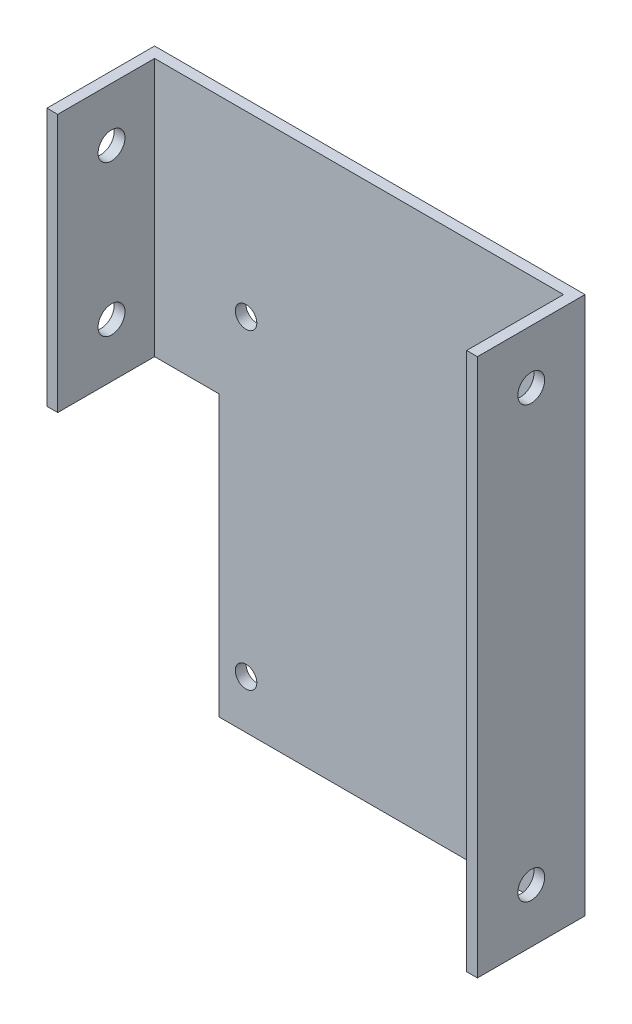
SolidWorks part; units mm, degrees
ref_plane "Alzado" through (0, 0, 0) normal (0, 0, 1) x (1, 0, 0)
ref_plane "Planta" through (0, 0, 0) normal (0, 1, 0) x (1, 0, 0)
ref_plane "Vista lateral" through (0, 0, 0) normal (1, 0, 0) x (0, 0, -1)
sketch "Sketch1" plane through (0, 0, 0) normal (0, 0, 1) x (1, 0, 0)
  line L1 (-15.7576, 19.8268) -> (24.2424, 19.8268)
  line L2 (-15.7576, 19.8268) -> (-15.7576, -30.1732)
  line L3 (-15.7576, -30.1732) -> (24.2424, -30.1732)
  line L4 (24.2424, 19.8268) -> (24.2424, -30.1732)
  dimension "D1" = 40
  dimension "D2" = 50
extrude "Boss-Extrude1" add sketch "Sketch1" along normal blind 1
sketch "Sketch2" plane through (0, 0, 1) normal (0, 0, 1) x (1, 0, 0)
  line L1 (-15.7576, -30.1732) -> (-10.7576, -30.1732)
  line L2 (-15.7576, -30.1732) -> (-15.7576, -5.1732)
  line L3 (-15.7576, -5.1732) -> (-10.7576, -5.1732)
  line L4 (-10.7576, -30.1732) -> (-10.7576, -5.1732)
  dimension "D1" = 5
  dimension "D2" = 25
extrude "Cut-Extrude1" cut sketch "Sketch2" against normal blind 1
sketch "Sketch3" plane through (0, 0, 0) normal (0, 0, -1) x (-1, 0, 0)
  line L0 (10.7576, -5.1732) -> (15.7576, -5.1732) construction
  line L1 (15.7576, 19.8268) -> (14.7576, 19.8268)
  line L2 (15.7576, 19.8268) -> (15.7576, -5.1732)
  line L3 (15.7576, -5.1732) -> (14.7576, -5.1732)
  line L4 (14.7576, 19.8268) -> (14.7576, -5.1732)
  line L6 (-24.2424, 19.8268) -> (-23.2424, 19.8268)
  line L7 (-24.2424, 19.8268) -> (-24.2424, -5.1732)
  line L8 (-24.2424, -5.1732) -> (-23.2424, -5.1732)
  line L9 (-23.2424, 19.8268) -> (-23.2424, -5.1732)
  dimension "D1" = 1
  dimension "D2" = 1
extrude "Boss-Extrude2" add sketch "Sketch3" against normal blind 10
sketch "Sketch4" plane through (24.2424, 0, 0) normal (1, 0, 0) x (0, 0, -1)
  line L0 (-10, 19.8268) -> (-10, -5.1732) construction
  line L1 (-10, -5.1732) -> (-1, -5.1732) construction
  line L2 (-10, 19.8268) -> (0, 19.8268) construction
  circle A0 centre (-5, -0.1732) radius 1.25
  circle A1 centre (-5, 14.8268) radius 1.25
  dimension "D1" = 2.5
  dimension "D4" = 2.5
  dimension "D2" = 5
  dimension "D3" = 5
  dimension "5" = 5
extrude "Cut-Extrude3" cut sketch "Sketch4" against normal blind 63
sketch "Sketch5" plane through (24.2424, 0, 0) normal (1, 0, 0) x (0, 0, -1)
  circle A0 centre (-5, -0.1732) radius 1.25
extrude "Boss-Extrude3" add sketch "Sketch5" against normal blind 1
sketch "Sketch6" plane through (0, 0, 10) normal (0, 0, 1) x (1, 0, 0)
  line L0 (-15.7576, -5.1732) -> (-15.7576, 19.8268) construction
  line L1 (24.2424, -5.1732) -> (-15.7576, -5.1732)
  line L2 (24.2424, -5.1732) -> (24.2424, 4.8268)
  line L3 (24.2424, 4.8268) -> (-15.7576, 4.8268)
  line L4 (-15.7576, -5.1732) -> (-15.7576, 4.8268)
  dimension "D1" = 10
extrude "Cut-Extrude4" cut sketch "Sketch6" against normal blind 9
sketch "Sketch7" plane through (-15.7576, 0, 0) normal (-1, 0, 0) x (0, 0, 1)
  line L0 (1, 4.8268) -> (10, 4.8268) construction
  circle A0 centre (5, 9.8268) radius 1.25
  dimension "D1" = 2.5
  dimension "D2" = 5
extrude "Cut-Extrude5" cut sketch "Sketch7" against normal blind 53
sketch "Sketch8" plane through (0, 0, 1) normal (0, 0, 1) x (1, 0, 0)
  line L0 (-10.7576, -30.1732) -> (24.2424, -30.1732) construction
  line L1 (-10.7576, -5.1732) -> (-8.7576, -5.1732)
  line L2 (-10.7576, -5.1732) -> (-10.7576, -30.1732)
  line L3 (-10.7576, -30.1732) -> (-8.7576, -30.1732)
  line L4 (-8.7576, -5.1732) -> (-8.7576, -30.1732)
  dimension "D1" = 2
extrude "Cut-Extrude6" cut sketch "Sketch8" against normal blind 53
sketch "Sketch9" plane through (0, 0, 1) normal (0, 0, 1) x (1, 0, 0)
  line L0 (-8.7576, -30.1732) -> (-8.7576, -5.1732) construction
  line L1 (-15.7576, -5.1732) -> (-8.7576, -5.1732)
  line L2 (-15.7576, -5.1732) -> (-15.7576, -3.1732)
  line L3 (-15.7576, -3.1732) -> (-8.7576, -3.1732)
  line L4 (-8.7576, -5.1732) -> (-8.7576, -3.1732)
  dimension "D1" = 2
extrude "Cut-Extrude8" cut sketch "Sketch9" against normal blind 53
sketch "Sketch10" plane through (24.2424, 0, 0) normal (1, 0, 0) x (0, 0, -1)
  line L0 (-1, -30.1732) -> (-1, 4.8268) construction
  line L1 (-10, 4.8268) -> (-1, 4.8268)
  line L2 (-10, 4.8268) -> (-10, -15.8236)
  line L3 (-10, -15.8236) -> (-1, -15.8236)
  line L4 (-1, 4.8268) -> (-1, -15.8236)
extrude "Boss-Extrude4" add sketch "Sketch10" against normal blind 1
sketch "Sketch11" plane through (24.2424, 0, 0) normal (1, 0, 0) x (0, 0, -1)
  line L0 (-10, -15.8236) -> (-1, -15.8236) construction
  line L1 (0, -30.1732) -> (0, 19.8268) construction
  circle A0 centre (-5, -10.8236) radius 1.25
  dimension "D1" = 5
  dimension "D2" = 5
extrude "Cut-Extrude9" cut sketch "Sketch11" against normal blind 1
sketch "Sketch12" plane through (24.2424, 0, 0) normal (1, 0, 0) x (0, 0, -1)
  circle A0 centre (-5, 9.8268) radius 1.25
extrude "Boss-Extrude5" add sketch "Sketch12" against normal blind 1
sketch "Sketch13" plane through (-15.7576, 0, 0) normal (-1, 0, 0) x (0, 0, 1)
  circle A0 centre (5, 9.8268) radius 1.25
extrude "Boss-Extrude6" add sketch "Sketch13" against normal blind 1
sketch "Sketch14" plane through (0, 0, 1) normal (0, 0, 1) x (1, 0, 0)
  line L0 (-8.7576, -30.1732) -> (-8.7576, -3.1732) construction
  line L1 (-15.7576, -3.1732) -> (-8.7576, -3.1732)
  line L2 (-15.7576, -3.1732) -> (-15.7576, -4.1732)
  line L3 (-15.7576, -4.1732) -> (-8.7576, -4.1732)
  line L4 (-8.7576, -3.1732) -> (-8.7576, -4.1732)
  dimension "D1" = 1
extrude "Boss-Extrude7" add sketch "Sketch14" against normal blind 1
sketch "Sketch15" plane through (0, 0, 1) normal (0, 0, 1) x (1, 0, 0)
  line L1 (-15.7576, -4.1732) -> (-14.7576, -4.1732)
  line L2 (-15.7576, -4.1732) -> (-15.7576, 4.8268)
  line L3 (-15.7576, 4.8268) -> (-14.7576, 4.8268)
  line L4 (-14.7576, -4.1732) -> (-14.7576, 4.8268)
extrude "Boss-Extrude8" add sketch "Sketch15" along normal blind 9
sketch "Sketch16" plane through (-15.7576, 0, 0) normal (-1, 0, 0) x (0, 0, 1)
  line L0 (0, -4.1732) -> (10, -4.1732) construction
  circle A0 centre (5, 14.8268) radius 1.25
  circle A1 centre (5, 0.8268) radius 1.25
  dimension "D1" = 5
extrude "Cut-Extrude10" cut sketch "Sketch16" against normal blind 9
sketch "Sketch17" plane through (0, 0, 1) normal (0, 0, 1) x (1, 0, 0)
  line L0 (23.2424, -15.8236) -> (23.2424, 19.8268) construction
  line L1 (24.2424, -30.1732) -> (23.2424, -30.1732)
  line L2 (24.2424, -30.1732) -> (24.2424, 1.2337)
  line L3 (24.2424, 1.2337) -> (23.2424, 1.2337)
  line L4 (23.2424, -30.1732) -> (23.2424, 1.2337)
extrude "Boss-Extrude9" add sketch "Sketch17" along normal blind 9
sketch "Sketch18" plane through (24.2424, 0, 0) normal (1, 0, 0) x (0, 0, -1)
  line L0 (-10, -30.1732) -> (0, -30.1732) construction
  circle A1 centre (-5, -25.1732) radius 1.25
  dimension "D1" = 5
extrude "Cut-Extrude11" cut sketch "Sketch18" against normal blind 9
sketch "Sketch19" plane through (0, 0, 1) normal (0, 0, 1) x (1, 0, 0)
  line L0 (24.2424, 19.8268) -> (24.2424, -30.1732) construction
  line L1 (-8.7576, -30.1732) -> (24.2424, -30.1732)
  line L2 (-8.7576, -30.1732) -> (-8.7576, -29.1732)
  line L3 (-8.7576, -29.1732) -> (24.2424, -29.1732)
  line L4 (24.2424, -30.1732) -> (24.2424, -29.1732)
  dimension "D1" = 1
extrude "Boss-Extrude10" add sketch "Sketch19" along normal blind 9
sketch "Sketch20" plane through (0, -30.1732, 0) normal (0, -1, 0) x (1, 0, 0)
  line L0 (-8.7576, 0) -> (24.2424, 0) construction
  line L1 (-8.7576, 0) -> (-8.7576, 10) construction
  line L2 (24.2424, 10) -> (24.2424, 0) construction
  circle A0 centre (-3.7576, 5) radius 1.25
  circle A1 centre (19.2424, 5) radius 1.25
  dimension "D1" = 5
  dimension "D3" = 5
  dimension "D2" = 5
extrude "Cut-Extrude12" cut sketch "Sketch20" against normal blind 9
sketch "Sketch21" plane through (0, 0, 0) normal (0, 0, -1) x (-1, 0, 0)
  circle A0 centre (-21.7424, 3.3268) radius 1
  circle A1 centre (6.2576, 3.2785) radius 1
  circle A2 centre (6.2576, -25.6732) radius 1
  circle A3 centre (-21.7424, -25.6732) radius 1
  point P4 (-7.7424, -11.1732)
extrude "Cut-Extrude13" cut sketch "Sketch21" against normal blind 10
sketch "Sketch22" plane through (0, 0, 10) normal (0, 0, 1) x (1, 0, 0)
  line L1 (24.2424, -30.1732) -> (-8.7576, -30.1732)
  line L2 (24.2424, -30.1732) -> (24.2424, -29.1732)
  line L3 (24.2424, -29.1732) -> (-8.7576, -29.1732)
  line L4 (-8.7576, -30.1732) -> (-8.7576, -29.1732)
extrude "Cut-Extrude14" cut sketch "Sketch22" against normal up to vertex (9 mm away)
sketch "Sketch23" plane through (0, 0, 1) normal (0, 0, 1) x (1, 0, 0)
  line L1 (24.2424, -30.1732) -> (23.2424, -30.1732)
  line L2 (24.2424, -30.1732) -> (24.2424, -29.1732)
  line L3 (24.2424, -29.1732) -> (23.2424, -29.1732)
  line L4 (23.2424, -30.1732) -> (23.2424, -29.1732)
extrude "Boss-Extrude11" add sketch "Sketch23" along normal up to vertex (9 mm away)
